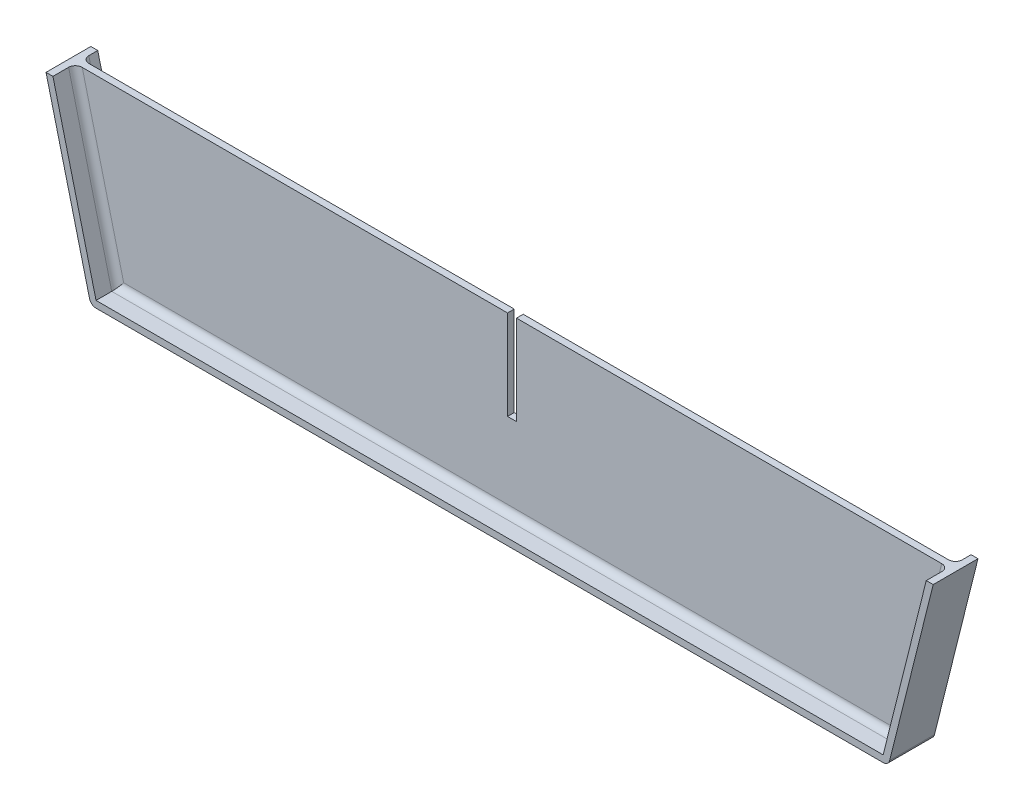
SolidWorks part; units mm, degrees
ref_plane "Front Plane" through (0, 0, 0) normal (0, 0, 1) x (1, 0, 0)
ref_plane "Top Plane" through (0, 0, 0) normal (0, 1, 0) x (1, 0, 0)
ref_plane "Right Plane" through (0, 0, 0) normal (1, 0, 0) x (0, 0, -1)
sketch "Sketch1" plane through (0, 0, 0) normal (0, 0, 1) x (1, 0, 0)
  line L0 (0, 0) -> (98, 0)
  line L1 (188, -40) -> (198, 0)
  line L2 (10, -40) -> (188, -40)
  line L3 (0, 0) -> (10, -40)
  line L4 (100, 0) -> (198, 0)
  line L6 (98, 0) -> (98, -20)
  line L7 (98, -20) -> (100, -20)
  line L8 (100, 0) -> (100, -20)
  point P4 (99, -40)
  dimension "D1" = 198
  dimension "D2" = 178
  dimension "D3" = 40
  dimension "D4" = 99
  dimension "D5" = 98
  dimension "D6" = 2
  dimension "D7" = 20
extrude "Boss-Extrude2" add sketch "Sketch1" along normal blind 1.5
sketch "Sketch5" plane through (0, 0, 1.5) normal (0, 0, 1) x (1, 0, 0)
  line L14 (98, 0) -> (0, 0) construction
  line L15 (198, 0) -> (100, 0) construction
  line L16 (188, -40) -> (198, 0) construction
  line L17 (186.8288, -38.5) -> (196.5448, 0.3638)
  line L18 (11.1712, -38.5) -> (186.8288, -38.5)
  line L19 (1.4552, 0.3638) -> (11.1712, -38.5)
  line L20 (186.8288, -38.5) -> (196.4538, 0)
  line L21 (11.1712, -38.5) -> (186.8288, -38.5)
  line L22 (1.5462, 0) -> (11.1712, -38.5)
  line L23 (10, -40) -> (188, -40) construction
  line L24 (0, 0) -> (10, -40) construction
  line L25 (188, -40) -> (198, 0)
  line L26 (10, -40) -> (188, -40)
  line L27 (0, 0) -> (10, -40)
  line L28 (196.4538, 0) -> (198, 0)
  line L29 (1.5462, 0) -> (0, 0)
  dimension "D1" = 1.5
extrude "Boss-Extrude3" add sketch "Sketch5" along normal blind 5 and the other way blind 5
fillet "Fillet1" radius 1.5 8 edges at (6.3587, -19.25, 1.5) (99, -38.5, 1.5) (191.6413, -19.25, 1.5) (191.6413, -19.25, 0) (99, -38.5, 0) (6.3587, -19.25, 0) (10, -40, 1.5) (188, -40, 1.5)
equation "\"bl1\"=90"
equation "\"bw1\"=70"
